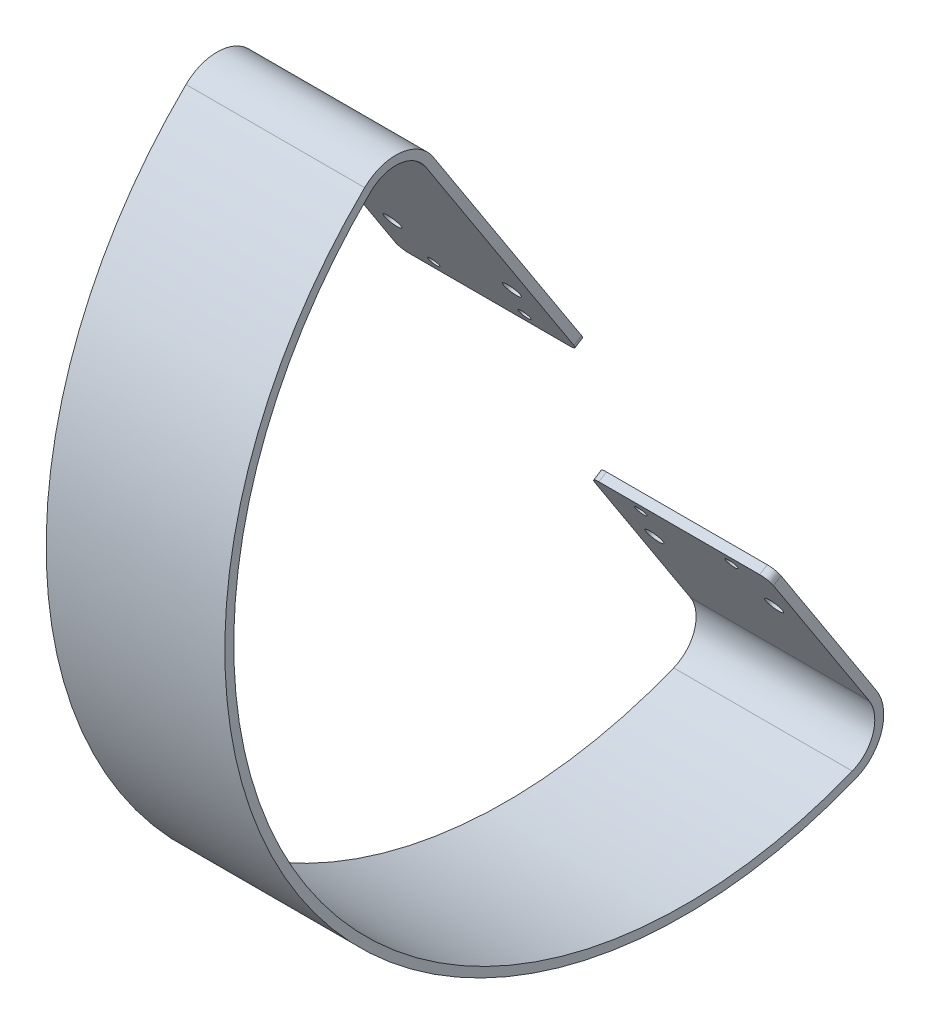
SolidWorks part; units mm, degrees
ref_plane "Front Plane" through (0, 0, 0) normal (0, 0, 1) x (1, 0, 0)
ref_plane "Top Plane" through (0, 0, 0) normal (0, 1, 0) x (1, 0, 0)
ref_plane "Right Plane" through (0, 0, 0) normal (1, 0, 0) x (0, 0, -1)
ref_plane "Plane1" through (1981.2, 0, 0) normal (1, 0, 0) x (0, 0, -1)
sketch "Sketch2" plane through (1981.2, 0, 0) normal (1, 0, 0) x (0, 0, -1)
  line L0 (221.3296, 149.9357) -> (209.5008, 142.2673) construction
  line L1 (221.3296, 149.9357) -> (209.184, 168.6708) construction
  line L2 (221.3296, 149.9357) -> (209.184, 168.6708) construction
  line L3 (273.5917, 69.3195) -> (285.7374, 50.5844) construction
  line L4 (273.5917, 69.3195) -> (285.7374, 50.5844) construction
  line L5 (220.4661, 151.2678) -> (176.9489, 218.3946)
  line L6 (274.4553, 67.9874) -> (303.0021, 23.953)
  line L7 (313.9939, 6.9977) -> (307.8258, 16.5121) construction
  line L8 (273.5917, 69.3195) -> (265.5737, 64.1215) construction
  line L9 (165.7975, 235.5961) -> (172.2848, 225.5893) construction
  line L10 (247.9458, 109.942) -> (151.6337, 47.5045) construction
  line L11 (151.6337, 47.5045) -> (142.0377, 41.2836) construction
  arc A0 (157.4526, 220.6047) -> (297.0616, 5.2526) centre (248.4911, 126.6943) ccw
  arc A1 (297.0616, 5.2526) -> (303.0021, 23.953) centre (292.3455, 17.0445) ccw
  arc A2 (176.9489, 218.3946) -> (157.4526, 220.6047) centre (166.2923, 211.4861) ccw
  spline S11 degree 3 poles (716.4378, 3936.626) (-41.01, 922.5586) (-45.8421, 102.7973) (199.57, -1.0271) (203.7349, -2.5525) (212.2057, -5.1923) (216.5116, -6.3067) (221.9842, -7.4366) (223.0832, -7.6494) (225.2905, -8.0483) (226.4002, -8.2347) (229.7298, -8.7513) (231.9491, -9.0392) (238.6058, -9.7364) (247.4783, -10.2233) (256.3445, -9.8408) (262.9919, -9.2245) (265.2072, -8.964) (268.5297, -8.4895) (269.6371, -8.3173) (271.8517, -7.9447) (272.9592, -7.7441) (278.4654, -6.6762) (282.7945, -5.61) (291.3052, -3.0674) (295.4869, -1.5909) (303.7034, 1.7715) (307.7383, 3.6574) (313.6773, 6.8016) (315.6425, 7.9051) (319.4945, 10.1955) (321.3853, 11.3842) (326.954, 15.0783) (334.1028, 20.3445) (340.7075, 26.2822) (345.4543, 30.9907) (347.0021, 32.6028) (349.271, 35.086) (350.0194, 35.9257) (351.4935, 37.6212) (352.2185, 38.4763) (355.7849, 42.7884) (358.4496, 46.3546) (363.4124, 53.7139) (365.7105, 57.5069) (369.9395, 65.3203) (371.8705, 69.3405) (374.0477, 74.5122) (374.4716, 75.5549) (375.2914, 77.6441) (375.6877, 78.6918) (376.8361, 81.8437) (377.548, 83.9569) (379.5247, 90.3317) (381.7375, 98.9252) (383.1139, 107.7043) (383.8268, 114.3594) (384.0111, 116.5896) (384.206, 119.9531) (384.2572, 121.077) (384.3321, 123.3185) (384.3557, 124.4376) (384.4056, 130.025) (384.2279, 134.4691) (383.4468, 143.3067) (382.8435, 147.7002) (381.2088, 156.4363) (380.1775, 160.7789) (378.6114, 166.1743) (378.2848, 167.25) (377.6073, 169.3868) (377.2561, 170.4491) (376.1655, 173.6179) (375.3891, 175.7062) (372.914, 181.8996) (371.0697, 185.9333) (366.9956, 193.8116) (364.7657, 197.6562) (361.1252, 203.278) (359.8623, 205.1277) (357.2357, 208.7777) (355.8817, 210.5644) (351.7057, 215.8037) (348.7675, 219.1395) (342.5889, 225.5033) (339.3485, 228.5312) (332.5628, 234.2766) (329.0156, 236.9953) (49.0165, 430.2441) (-881.9041, -433.1454) (-2551.1811, -2485.4465) knots -1.810739 -1.810739 -1.810739 -1.810739 0.03125 0.03125 0.0625 0.0625 0.09375 0.09375 0.101562 0.101562 0.109375 0.109375 0.125 0.125 0.15625 0.1875 0.1875 0.203125 0.203125 0.210937 0.210937 0.21875 0.21875 0.25 0.25 0.28125 0.28125 0.3125 0.3125 0.328125 0.328125 0.34375 0.34375 0.375 0.40625 0.40625 0.421875 0.421875 0.429687 0.429687 0.4375 0.4375 0.46875 0.46875 0.5 0.5 0.53125 0.53125 0.539063 0.539063 0.546875 0.546875 0.5625 0.5625 0.59375 0.625 0.625 0.640625 0.640625 0.648438 0.648438 0.65625 0.65625 0.6875 0.6875 0.71875 0.71875 0.75 0.75 0.757813 0.757813 0.765625 0.765625 0.78125 0.78125 0.8125 0.8125 0.84375 0.84375 0.859375 0.859375 0.875 0.875 0.90625 0.90625 0.9375 0.9375 0.96875 0.96875 3.30132 3.30132 3.30132 3.30132 only from (183.4088, 6.5279) to (313.8564, 246.6465)
  spline S12 degree 3 poles (183.4088, 6.5279) (187.3587, 4.3756) (191.3819, 2.437) (199.57, -1.0271) (203.7349, -2.5525) (212.2057, -5.1923) (216.5116, -6.3067) (221.9842, -7.4366) (223.0832, -7.6494) (225.2905, -8.0483) (226.4002, -8.2347) (229.7298, -8.7513) (231.9491, -9.0392) (238.6058, -9.7364) (247.4783, -10.2233) (256.3445, -9.8408) (262.9919, -9.2245) (265.2072, -8.964) (268.5297, -8.4895) (269.6371, -8.3173) (271.8517, -7.9447) (272.9592, -7.7441) (278.4654, -6.6762) (282.7945, -5.61) (291.3052, -3.0674) (295.4869, -1.5909) (303.7034, 1.7715) (307.7383, 3.6574) (313.6773, 6.8016) (315.6425, 7.9051) (319.4945, 10.1955) (321.3853, 11.3842) (326.954, 15.0783) (334.1028, 20.3445) (340.7075, 26.2822) (345.4543, 30.9907) (347.0021, 32.6028) (349.271, 35.086) (350.0194, 35.9257) (351.4935, 37.6212) (352.2185, 38.4763) (355.7849, 42.7884) (358.4496, 46.3546) (363.4124, 53.7139) (365.7105, 57.5069) (369.9395, 65.3203) (371.8705, 69.3405) (374.0477, 74.5122) (374.4716, 75.5549) (375.2914, 77.6441) (375.6877, 78.6918) (376.8361, 81.8437) (377.548, 83.9569) (379.5247, 90.3317) (381.7375, 98.9252) (383.1139, 107.7043) (383.8268, 114.3594) (384.0111, 116.5896) (384.206, 119.9531) (384.2572, 121.077) (384.3321, 123.3185) (384.3557, 124.4376) (384.4056, 130.025) (384.2279, 134.4691) (383.4468, 143.3067) (382.8435, 147.7002) (381.2088, 156.4363) (380.1775, 160.7789) (378.6114, 166.1743) (378.2848, 167.25) (377.6073, 169.3868) (377.2561, 170.4491) (376.1655, 173.6179) (375.3891, 175.7062) (372.914, 181.8996) (371.0697, 185.9333) (366.9956, 193.8116) (364.7657, 197.6562) (361.1252, 203.278) (359.8623, 205.1277) (357.2357, 208.7777) (355.8817, 210.5644) (351.7057, 215.8037) (348.7675, 219.1395) (342.5889, 225.5033) (339.3485, 228.5312) (332.5628, 234.2766) (329.0156, 236.9953) (321.6123, 242.1048) (317.7932, 244.4704) (313.8564, 246.6465) knots 0 0 0 0 0.03125 0.03125 0.0625 0.0625 0.09375 0.09375 0.101562 0.101562 0.109375 0.109375 0.125 0.125 0.15625 0.1875 0.1875 0.203125 0.203125 0.210937 0.210937 0.21875 0.21875 0.25 0.25 0.28125 0.28125 0.3125 0.3125 0.328125 0.328125 0.34375 0.34375 0.375 0.40625 0.40625 0.421875 0.421875 0.429687 0.429687 0.4375 0.4375 0.46875 0.46875 0.5 0.5 0.53125 0.53125 0.539063 0.539063 0.546875 0.546875 0.5625 0.5625 0.59375 0.625 0.625 0.640625 0.640625 0.648438 0.648438 0.65625 0.65625 0.6875 0.6875 0.71875 0.71875 0.75 0.75 0.757813 0.757813 0.765625 0.765625 0.78125 0.78125 0.8125 0.8125 0.84375 0.84375 0.859375 0.859375 0.875 0.875 0.90625 0.90625 0.9375 0.9375 0.96875 0.96875 1 1 1 1 construction
  spline S13 degree 3 poles (-242.5395, -3680.1608) (532.8048, -671.0788) (542.6093, 149.0677) (297.6784, 254.3238) (293.5061, 255.8778) (285.0171, 258.5726) (280.7003, 259.7133) (275.2117, 260.8746) (274.1094, 261.0936) (271.8953, 261.5048) (270.782, 261.6972) (267.443, 262.2314) (265.217, 262.5306) (258.5394, 263.2607) (249.6363, 263.7882) (240.7343, 263.4398) (234.0581, 262.8463) (231.8328, 262.593) (228.4949, 262.1285) (227.3823, 261.9595) (225.1571, 261.5931) (224.0452, 261.3957) (218.5166, 260.3429) (214.169, 259.2871) (205.6195, 256.7613) (201.4177, 255.2913) (193.1597, 251.9376) (189.1035, 250.054) (183.1315, 246.9097) (181.1566, 245.8063) (177.2874, 243.5165) (175.3879, 242.3277) (169.7931, 238.6317) (162.6093, 233.359) (155.9696, 227.4065) (151.1969, 222.6832) (149.6406, 221.0656) (147.359, 218.5732) (146.6064, 217.7303) (145.1266, 216.0311) (144.3986, 215.1739) (140.818, 210.8513) (138.1421, 207.2748) (133.1582, 199.8912) (130.8502, 196.0841) (126.6032, 188.2385) (124.6641, 184.2) (122.4784, 179.0026) (122.0536, 177.9566) (121.2326, 175.8611) (120.8357, 174.8103) (119.6855, 171.6484) (118.9728, 169.5282) (116.994, 163.1312) (115.8872, 158.8181) (114.0946, 150.0958) (113.4088, 145.6866) (112.7023, 138.9994) (112.5206, 136.758) (112.2671, 132.2503) (112.1964, 130.0028) (112.1486, 123.2788) (112.3356, 118.8209) (113.1385, 109.9533) (113.7544, 105.5437) (115.0024, 98.9659) (115.4726, 96.7794) (116.2603, 93.5089) (116.5366, 92.4203) (117.117, 90.2462) (117.4215, 89.1595) (119.0097, 83.7486) (120.4827, 79.5175) (123.8202, 71.2447) (125.6848, 67.2028) (129.8041, 59.3075) (132.0588, 55.454) (135.127, 50.7579) (135.7532, 49.8247) (137.0308, 47.9705) (137.6833, 47.0483) (139.6701, 44.3124) (141.0345, 42.5284) (145.2445, 37.2943) (151.1692, 30.6289) (157.7065, 24.5799) (162.8419, 20.2771) (164.5926, 18.8819) (167.2777, 16.8487) (168.1826, 16.1809) (170.0125, 14.8654) (170.9378, 14.2174) (443.8284, -171.8536) (1345.0037, 655.8308) (3034.7171, 2753.1631) knots -1.804531 -1.804531 -1.804531 -1.804531 0.03125 0.03125 0.0625 0.0625 0.09375 0.09375 0.101562 0.101562 0.109375 0.109375 0.125 0.125 0.15625 0.1875 0.1875 0.203125 0.203125 0.210937 0.210937 0.21875 0.21875 0.25 0.25 0.28125 0.28125 0.3125 0.3125 0.328125 0.328125 0.34375 0.34375 0.375 0.40625 0.40625 0.421875 0.421875 0.429687 0.429687 0.4375 0.4375 0.46875 0.46875 0.5 0.5 0.53125 0.53125 0.539062 0.539062 0.546875 0.546875 0.5625 0.5625 0.59375 0.59375 0.625 0.625 0.640625 0.640625 0.65625 0.65625 0.6875 0.6875 0.71875 0.71875 0.734375 0.734375 0.742187 0.742187 0.75 0.75 0.78125 0.78125 0.8125 0.8125 0.84375 0.84375 0.851562 0.851562 0.859375 0.859375 0.875 0.875 0.90625 0.9375 0.9375 0.953125 0.953125 0.960937 0.960937 0.96875 0.96875 3.24847 3.24847 3.24847 3.24847 only from (313.8564, 246.6465) to (183.4088, 6.5279)
  spline S14 degree 3 poles (313.8564, 246.6465) (309.9046, 248.8308) (305.8776, 250.8003) (297.6784, 254.3238) (293.5061, 255.8778) (285.0171, 258.5726) (280.7003, 259.7133) (275.2117, 260.8746) (274.1094, 261.0936) (271.8953, 261.5048) (270.782, 261.6972) (267.443, 262.2314) (265.217, 262.5306) (258.5394, 263.2607) (249.6363, 263.7882) (240.7343, 263.4398) (234.0581, 262.8463) (231.8328, 262.593) (228.4949, 262.1285) (227.3823, 261.9595) (225.1571, 261.5931) (224.0452, 261.3957) (218.5166, 260.3429) (214.169, 259.2871) (205.6195, 256.7613) (201.4177, 255.2913) (193.1597, 251.9376) (189.1035, 250.054) (183.1315, 246.9097) (181.1566, 245.8063) (177.2874, 243.5165) (175.3879, 242.3277) (169.7931, 238.6317) (162.6093, 233.359) (155.9696, 227.4065) (151.1969, 222.6832) (149.6406, 221.0656) (147.359, 218.5732) (146.6064, 217.7303) (145.1266, 216.0311) (144.3986, 215.1739) (140.818, 210.8513) (138.1421, 207.2748) (133.1582, 199.8912) (130.8502, 196.0841) (126.6032, 188.2385) (124.6641, 184.2) (122.4784, 179.0026) (122.0536, 177.9566) (121.2326, 175.8611) (120.8357, 174.8103) (119.6855, 171.6484) (118.9728, 169.5282) (116.994, 163.1312) (115.8872, 158.8181) (114.0946, 150.0958) (113.4088, 145.6866) (112.7023, 138.9994) (112.5206, 136.758) (112.2671, 132.2503) (112.1964, 130.0028) (112.1486, 123.2788) (112.3356, 118.8209) (113.1385, 109.9533) (113.7544, 105.5437) (115.0024, 98.9659) (115.4726, 96.7794) (116.2603, 93.5089) (116.5366, 92.4203) (117.117, 90.2462) (117.4215, 89.1595) (119.0097, 83.7486) (120.4827, 79.5175) (123.8202, 71.2447) (125.6848, 67.2028) (129.8041, 59.3075) (132.0588, 55.454) (135.127, 50.7579) (135.7532, 49.8247) (137.0308, 47.9705) (137.6833, 47.0483) (139.6701, 44.3124) (141.0345, 42.5284) (145.2445, 37.2943) (151.1692, 30.6289) (157.7065, 24.5799) (162.8419, 20.2771) (164.5926, 18.8819) (167.2777, 16.8487) (168.1826, 16.1809) (170.0125, 14.8654) (170.9378, 14.2174) (175.5978, 11.04) (179.444, 8.6885) (183.4088, 6.5279) knots 0 0 0 0 0.03125 0.03125 0.0625 0.0625 0.09375 0.09375 0.101562 0.101562 0.109375 0.109375 0.125 0.125 0.15625 0.1875 0.1875 0.203125 0.203125 0.210937 0.210937 0.21875 0.21875 0.25 0.25 0.28125 0.28125 0.3125 0.3125 0.328125 0.328125 0.34375 0.34375 0.375 0.40625 0.40625 0.421875 0.421875 0.429687 0.429687 0.4375 0.4375 0.46875 0.46875 0.5 0.5 0.53125 0.53125 0.539062 0.539062 0.546875 0.546875 0.5625 0.5625 0.59375 0.59375 0.625 0.625 0.640625 0.640625 0.65625 0.65625 0.6875 0.6875 0.71875 0.71875 0.734375 0.734375 0.742187 0.742187 0.75 0.75 0.78125 0.78125 0.8125 0.8125 0.84375 0.84375 0.851562 0.851562 0.859375 0.859375 0.875 0.875 0.90625 0.9375 0.9375 0.953125 0.953125 0.960937 0.960937 0.96875 0.96875 1 1 1 1 construction
  spline S15 degree 3 poles (-283.106, -3688.3408) (508.334, -662.837) (526.1426, 143.4053) (293.3653, 243.1749) (289.5491, 244.5923) (281.7849, 247.0493) (277.837, 248.0889) (272.8177, 249.1464) (271.8096, 249.3458) (269.7849, 249.7201) (268.7669, 249.8952) (265.7133, 250.3813) (263.6778, 250.6532) (257.5713, 251.316) (249.4303, 251.7922) (241.291, 251.468) (235.1872, 250.9213) (233.1527, 250.6884) (230.1011, 250.2617) (229.0839, 250.1066) (227.0497, 249.7703) (226.033, 249.5891) (220.9782, 248.6234) (217.0033, 247.6557) (209.1872, 245.3418) (205.3459, 243.9957) (197.7969, 240.9256) (194.0891, 239.2017) (188.6302, 236.3247) (186.8249, 235.315) (183.2875, 233.2197) (181.551, 232.132) (176.4364, 228.7505) (169.8693, 223.927) (163.7999, 218.4829) (159.4374, 214.1635) (158.0148, 212.6842) (155.9293, 210.4051) (155.2414, 209.6343) (153.8884, 208.0802) (153.2229, 207.2963) (149.9492, 203.3428) (147.5028, 200.0721) (142.9464, 193.3202) (140.8363, 189.8391) (136.9535, 182.6657) (135.1806, 178.9735) (133.1822, 174.2221) (132.7937, 173.2655) (132.0427, 171.3492) (131.6797, 170.3883) (130.6277, 167.4969) (129.9758, 165.5582) (128.1657, 159.7088) (127.1531, 155.7651) (125.5126, 147.7903) (124.8848, 143.7592) (124.2373, 137.6458) (124.0706, 135.5968) (123.8376, 131.4761) (123.7722, 129.4199) (123.7265, 123.2709) (123.896, 119.1943) (124.6269, 111.0857) (125.1883, 107.0537) (126.3265, 101.0393) (126.7553, 99.0401) (127.7134, 95.0532) (128.2432, 93.0636) (129.9829, 87.1241) (131.3277, 83.254) (134.375, 75.687) (136.0776, 71.9901) (139.8389, 64.7687) (141.8976, 61.2443) (144.6991, 56.9491) (145.2709, 56.0957) (146.4374, 54.3999) (147.0331, 53.5564) (148.8483, 51.0526) (150.0947, 49.42) (153.9409, 44.63) (159.3536, 38.5301) (165.3255, 32.9941) (170.0165, 29.0559) (171.6156, 27.7789) (174.0683, 25.9178) (174.8948, 25.3065) (176.5662, 24.1024) (177.4116, 23.509) (439.002, -155.2606) (1332.8814, 685.8356) (3014.0431, 2794.3665) knots -1.877287 -1.877287 -1.877287 -1.877287 0.03125 0.03125 0.0625 0.0625 0.09375 0.09375 0.101563 0.101563 0.109375 0.109375 0.125 0.125 0.15625 0.1875 0.1875 0.203125 0.203125 0.210938 0.210938 0.21875 0.21875 0.25 0.25 0.28125 0.28125 0.3125 0.3125 0.328125 0.328125 0.34375 0.34375 0.375 0.40625 0.40625 0.421875 0.421875 0.429688 0.429688 0.4375 0.4375 0.46875 0.46875 0.5 0.5 0.53125 0.53125 0.539063 0.539063 0.546875 0.546875 0.5625 0.5625 0.59375 0.59375 0.625 0.625 0.640625 0.640625 0.65625 0.65625 0.6875 0.6875 0.71875 0.71875 0.734375 0.734375 0.75 0.75 0.78125 0.78125 0.8125 0.8125 0.84375 0.84375 0.851563 0.851563 0.859375 0.859375 0.875 0.875 0.90625 0.9375 0.9375 0.953125 0.953125 0.960938 0.960938 0.96875 0.96875 3.360625 3.360625 3.360625 3.360625 only from (308.1647, 236.1696) to (188.8075, 16.4655)
  spline S16 degree 3 poles (308.1647, 236.1696) (304.5493, 238.1632) (300.8654, 239.9603) (293.3653, 243.1749) (289.5491, 244.5923) (281.7849, 247.0493) (277.837, 248.0889) (272.8177, 249.1464) (271.8096, 249.3458) (269.7849, 249.7201) (268.7669, 249.8952) (265.7133, 250.3813) (263.6778, 250.6532) (257.5713, 251.316) (249.4303, 251.7922) (241.291, 251.468) (235.1872, 250.9213) (233.1527, 250.6884) (230.1011, 250.2617) (229.0839, 250.1066) (227.0497, 249.7703) (226.033, 249.5891) (220.9782, 248.6234) (217.0033, 247.6557) (209.1872, 245.3418) (205.3459, 243.9957) (197.7969, 240.9256) (194.0891, 239.2017) (188.6302, 236.3247) (186.8249, 235.315) (183.2875, 233.2197) (181.551, 232.132) (176.4364, 228.7505) (169.8693, 223.927) (163.7999, 218.4829) (159.4374, 214.1635) (158.0148, 212.6842) (155.9293, 210.4051) (155.2414, 209.6343) (153.8884, 208.0802) (153.2229, 207.2963) (149.9492, 203.3428) (147.5028, 200.0721) (142.9464, 193.3202) (140.8363, 189.8391) (136.9535, 182.6657) (135.1806, 178.9735) (133.1822, 174.2221) (132.7937, 173.2655) (132.0427, 171.3492) (131.6797, 170.3883) (130.6277, 167.4969) (129.9758, 165.5582) (128.1657, 159.7088) (127.1531, 155.7651) (125.5126, 147.7903) (124.8848, 143.7592) (124.2373, 137.6458) (124.0706, 135.5968) (123.8376, 131.4761) (123.7722, 129.4199) (123.7265, 123.2709) (123.896, 119.1943) (124.6269, 111.0857) (125.1883, 107.0537) (126.3265, 101.0393) (126.7553, 99.0401) (127.7134, 95.0532) (128.2432, 93.0636) (129.9829, 87.1241) (131.3277, 83.254) (134.375, 75.687) (136.0776, 71.9901) (139.8389, 64.7687) (141.8976, 61.2443) (144.6991, 56.9491) (145.2709, 56.0957) (146.4374, 54.3999) (147.0331, 53.5564) (148.8483, 51.0526) (150.0947, 49.42) (153.9409, 44.63) (159.3536, 38.5301) (165.3255, 32.9941) (170.0165, 29.0559) (171.6156, 27.7789) (174.0683, 25.9178) (174.8948, 25.3065) (176.5662, 24.1024) (177.4116, 23.509) (181.6698, 20.599) (185.1844, 18.445) (188.8075, 16.4655) knots 0 0 0 0 0.03125 0.03125 0.0625 0.0625 0.09375 0.09375 0.101563 0.101563 0.109375 0.109375 0.125 0.125 0.15625 0.1875 0.1875 0.203125 0.203125 0.210938 0.210938 0.21875 0.21875 0.25 0.25 0.28125 0.28125 0.3125 0.3125 0.328125 0.328125 0.34375 0.34375 0.375 0.40625 0.40625 0.421875 0.421875 0.429688 0.429688 0.4375 0.4375 0.46875 0.46875 0.5 0.5 0.53125 0.53125 0.539063 0.539063 0.546875 0.546875 0.5625 0.5625 0.59375 0.59375 0.625 0.625 0.640625 0.640625 0.65625 0.65625 0.6875 0.6875 0.71875 0.71875 0.734375 0.734375 0.75 0.75 0.78125 0.78125 0.8125 0.8125 0.84375 0.84375 0.851563 0.851563 0.859375 0.859375 0.875 0.875 0.90625 0.9375 0.9375 0.953125 0.953125 0.960938 0.960938 0.96875 0.96875 1 1 1 1 construction
  spline S17 degree 3 poles (-2751.1525, 2792.7474) (1122.9295, -127.9602) (498.065, 247.5508) (102.2279, 91.7606) (97.9404, 89.9983) (91.5629, 87.2263) (89.446, 86.281) (86.29, 84.8167) (85.2412, 84.3208) (13.5509, 49.5235) (-37.8649, -30.7706) (1405.2472, -3686.3529) knots -22.187167 -22.187167 -22.187167 -22.187167 0.5 0.5 0.75 0.75 0.875 0.875 0.9375 0.9375 5.166072 5.166072 5.166072 5.166072 only from (132.7178, 102.9159) to (81.0819, 82.252)
  spline S18 degree 3 poles (132.7178, 102.9159) (123.9131, 99.9934) (115.171, 96.8546) (102.2279, 91.7606) (97.9404, 89.9983) (91.5629, 87.2263) (89.446, 86.281) (86.29, 84.8167) (85.2412, 84.3208) (83.1528, 83.3072) (82.1129, 82.7903) (81.0819, 82.252) knots 0 0 0 0 0.5 0.5 0.75 0.75 0.875 0.875 0.9375 0.9375 1 1 1 1 construction
  spline S19 degree 3 poles (764.9531, 3943.1565) (-14.832, 914.4258) (-29.4722, 108.4213) (203.5969, 9.5325) (207.4088, 8.132) (215.1622, 5.7075) (219.1037, 4.6835) (224.1135, 3.6445) (225.1196, 3.4487) (227.1403, 3.0817) (228.1562, 2.9102) (231.2042, 2.4345) (233.2358, 2.1693) (239.3299, 1.5259) (247.4528, 1.0737) (255.571, 1.4181) (261.6577, 1.9783) (263.6863, 2.2155) (266.7288, 2.6481) (267.7429, 2.8051) (269.7709, 3.1451) (270.785, 3.3281) (275.8265, 4.3028) (279.7904, 5.2766) (287.5837, 7.6004) (291.413, 8.9503) (298.9375, 12.0256) (302.6327, 13.7509) (308.0721, 16.6279) (309.8717, 17.6376) (313.3989, 19.7332) (315.1302, 20.8209) (320.2294, 24.2012) (326.7758, 29.0209) (332.8245, 34.4563) (337.1717, 38.7669) (338.5892, 40.2429) (340.6672, 42.5166) (341.3527, 43.2855) (342.7023, 44.8374) (343.3661, 45.6202) (346.6313, 49.5673) (349.0711, 52.832) (353.6151, 59.5695) (355.7193, 63.0423) (359.5915, 70.1966) (361.3595, 73.878) (363.3529, 78.6142) (363.7409, 79.5689) (364.4911, 81.4814) (364.8538, 82.4405) (365.9048, 85.326) (366.5562, 87.2606) (368.3651, 93.0968) (370.3898, 100.9649) (371.6483, 109.0038) (372.2996, 115.0983) (372.4678, 117.1407) (372.6454, 120.2209) (372.692, 121.2497) (372.7599, 123.3015) (372.7812, 124.3259) (372.8253, 129.4407) (372.6612, 133.5091) (371.9432, 141.5999) (371.3893, 145.6224) (369.8891, 153.6213) (368.9428, 157.5976) (367.2188, 163.5263) (366.5969, 165.4835) (365.2638, 169.3503) (364.552, 171.2616) (362.2831, 176.9303) (360.5926, 180.6223) (356.858, 187.8336) (354.8139, 191.3527) (351.4766, 196.4989) (350.3187, 198.1924) (347.911, 201.5331) (346.671, 203.1668) (342.8449, 207.9599) (337.4608, 214.0634) (331.5223, 219.6036) (326.8586, 223.5454) (325.269, 224.8237) (322.0186, 227.3081) (320.3563, 228.5151) (55.1067, 411.2126) (-858.655, -454.0579) (-2525.9478, -2532.4739) knots -1.881423 -1.881423 -1.881423 -1.881423 0.03125 0.03125 0.0625 0.0625 0.09375 0.09375 0.101562 0.101562 0.109375 0.109375 0.125 0.125 0.15625 0.1875 0.1875 0.203125 0.203125 0.210938 0.210938 0.21875 0.21875 0.25 0.25 0.28125 0.28125 0.3125 0.3125 0.328125 0.328125 0.34375 0.34375 0.375 0.40625 0.40625 0.421875 0.421875 0.429687 0.429687 0.4375 0.4375 0.46875 0.46875 0.5 0.5 0.53125 0.53125 0.539062 0.539062 0.546875 0.546875 0.5625 0.5625 0.59375 0.625 0.625 0.640625 0.640625 0.648437 0.648437 0.65625 0.65625 0.6875 0.6875 0.71875 0.71875 0.75 0.75 0.765625 0.765625 0.78125 0.78125 0.8125 0.8125 0.84375 0.84375 0.859375 0.859375 0.875 0.875 0.90625 0.9375 0.9375 0.953125 0.953125 0.96875 0.96875 3.397555 3.397555 3.397555 3.397555 only from (188.8075, 16.4655) to (308.1647, 236.1696)
  spline S20 degree 3 poles (188.8075, 16.4655) (192.4217, 14.4908) (196.1034, 12.7119) (203.5969, 9.5325) (207.4088, 8.132) (215.1622, 5.7075) (219.1037, 4.6835) (224.1135, 3.6445) (225.1196, 3.4487) (227.1403, 3.0817) (228.1562, 2.9102) (231.2042, 2.4345) (233.2358, 2.1693) (239.3299, 1.5259) (247.4528, 1.0737) (255.571, 1.4181) (261.6577, 1.9783) (263.6863, 2.2155) (266.7288, 2.6481) (267.7429, 2.8051) (269.7709, 3.1451) (270.785, 3.3281) (275.8265, 4.3028) (279.7904, 5.2766) (287.5837, 7.6004) (291.413, 8.9503) (298.9375, 12.0256) (302.6327, 13.7509) (308.0721, 16.6279) (309.8717, 17.6376) (313.3989, 19.7332) (315.1302, 20.8209) (320.2294, 24.2012) (326.7758, 29.0209) (332.8245, 34.4563) (337.1717, 38.7669) (338.5892, 40.2429) (340.6672, 42.5166) (341.3527, 43.2855) (342.7023, 44.8374) (343.3661, 45.6202) (346.6313, 49.5673) (349.0711, 52.832) (353.6151, 59.5695) (355.7193, 63.0423) (359.5915, 70.1966) (361.3595, 73.878) (363.3529, 78.6142) (363.7409, 79.5689) (364.4911, 81.4814) (364.8538, 82.4405) (365.9048, 85.326) (366.5562, 87.2606) (368.3651, 93.0968) (370.3898, 100.9649) (371.6483, 109.0038) (372.2996, 115.0983) (372.4678, 117.1407) (372.6454, 120.2209) (372.692, 121.2497) (372.7599, 123.3015) (372.7812, 124.3259) (372.8253, 129.4407) (372.6612, 133.5091) (371.9432, 141.5999) (371.3893, 145.6224) (369.8891, 153.6213) (368.9428, 157.5976) (367.2188, 163.5263) (366.5969, 165.4835) (365.2638, 169.3503) (364.552, 171.2616) (362.2831, 176.9303) (360.5926, 180.6223) (356.858, 187.8336) (354.8139, 191.3527) (351.4766, 196.4989) (350.3187, 198.1924) (347.911, 201.5331) (346.671, 203.1668) (342.8449, 207.9599) (337.4608, 214.0634) (331.5223, 219.6036) (326.8586, 223.5454) (325.269, 224.8237) (322.0186, 227.3081) (320.3563, 228.5151) (315.2698, 232.0185) (311.7712, 234.1809) (308.1647, 236.1696) knots 0 0 0 0 0.03125 0.03125 0.0625 0.0625 0.09375 0.09375 0.101562 0.101562 0.109375 0.109375 0.125 0.125 0.15625 0.1875 0.1875 0.203125 0.203125 0.210938 0.210938 0.21875 0.21875 0.25 0.25 0.28125 0.28125 0.3125 0.3125 0.328125 0.328125 0.34375 0.34375 0.375 0.40625 0.40625 0.421875 0.421875 0.429687 0.429687 0.4375 0.4375 0.46875 0.46875 0.5 0.5 0.53125 0.53125 0.539062 0.539062 0.546875 0.546875 0.5625 0.5625 0.59375 0.625 0.625 0.640625 0.640625 0.648437 0.648437 0.65625 0.65625 0.6875 0.6875 0.71875 0.71875 0.75 0.75 0.765625 0.765625 0.78125 0.78125 0.8125 0.8125 0.84375 0.84375 0.859375 0.859375 0.875 0.875 0.90625 0.9375 0.9375 0.953125 0.953125 0.96875 0.96875 1 1 1 1 construction
  spline S21 degree 3 poles (2769.9179, -2964.6264) (54.3339, -168.8273) (38.2566, -57.489) (83.8558, -5.9808) (84.5785, -5.1969) (86.7794, -2.8779) (88.2901, -1.3751) (91.3667, 1.5757) (92.9329, 3.0232) (96.1079, 5.8762) (97.7165, 7.2812) (102.5853, 11.4344) (105.8915, 14.125) (112.6011, 19.3806) (116.0049, 21.9449) (122.8996, 26.9607) (126.3922, 29.4128) (133.4527, 34.2065) (137.0182, 36.5462) (646.9668, 360.422) (1813.8639, -388.0279) (148.3469, 3451.8328) knots -1.951853 -1.951853 -1.951853 -1.951853 0.03125 0.03125 0.0625 0.0625 0.125 0.125 0.1875 0.1875 0.25 0.25 0.375 0.375 0.5 0.5 0.625 0.625 0.75 0.75 18.337148 18.337148 18.337148 18.337148 only from (81.0819, -9.2325) to (162.6006, 51.9137)
  spline S22 degree 3 poles (81.0819, -9.2325) (81.7487, -8.3931) (82.4409, -7.5789) (83.8558, -5.9808) (84.5785, -5.1969) (86.7794, -2.8779) (88.2901, -1.3751) (91.3667, 1.5757) (92.9329, 3.0232) (96.1079, 5.8762) (97.7165, 7.2812) (102.5853, 11.4344) (105.8915, 14.125) (112.6011, 19.3806) (116.0049, 21.9449) (122.8996, 26.9607) (126.3922, 29.4128) (133.4527, 34.2065) (137.0182, 36.5462) (147.8148, 43.4033) (155.1459, 47.7585) (162.6006, 51.9137) knots 0 0 0 0 0.03125 0.03125 0.0625 0.0625 0.125 0.125 0.1875 0.1875 0.25 0.25 0.375 0.375 0.5 0.5 0.625 0.625 0.75 0.75 1 1 1 1 construction
  spline S23 degree 3 poles (207.2453, 83.5564) (260.0163, 2.1551) (341.4175, 54.9261) (288.6465, 136.3274) (235.8755, 217.7287) (154.4742, 164.9577) (207.2453, 83.5564) (260.0163, 2.1551) (341.4175, 54.9261) knots -0.5 0 0 0 0.5 0.5 0.5 1 1 1 1.5 1.5 1.5 weights 1 0.333333 0.333333 1 0.333333 0.333333 1 0.333333 0.333333 only from (207.2453, 83.5564) to (207.2453, 83.5564) construction
  spline S24 degree 3 poles (207.2453, 83.5564) (260.0163, 2.1551) (341.4175, 54.9261) (288.6465, 136.3274) (235.8755, 217.7287) (154.4742, 164.9577) (207.2453, 83.5564) (260.0163, 2.1551) (341.4175, 54.9261) knots -0.5 0 0 0 0.5 0.5 0.5 1 1 1 1.5 1.5 1.5 weights 1 0.333333 0.333333 1 0.333333 0.333333 1 0.333333 0.333333 only from (207.2453, 83.5564) to (207.2453, 83.5564) construction
  point P19 (169.0411, 230.5927)
  point P22 (310.9099, 11.7549)
  point P29 (146.8357, 44.394)
  point P33 (310.9099, 11.7549)
  point P36 (169.0411, 230.5927)
  dimension "D4" = 12.7
  dimension "D1" = 0
  dimension "D2" = 1.5875
  dimension "D3" = 1.5875
extrude "Extrude-Thin1" add sketch "Sketch2" along normal mid plane 50.8 thin contours L5 A2 A0 A1 L6
sketch "Sketch5" plane through (0, 145.3932, -224.2745) normal (0, 0.544, -0.8391) x (-1, 0, 0)
  ellipse E0 centre (-1997.9063, -111.0782) end of major axis (-2000.2876, -111.0782) minor radius 2.3812 construction
  ellipse E1 centre (-1963.9063, -111.0783) end of major axis (-1966.2876, -111.0783) minor radius 2.3812 construction
  ellipse E2 centre (-1967.8405, -96.6615) end of major axis (-1966.2898, -96.6615) minor radius 1.5506 construction
  ellipse E3 centre (-1993.6563, -96.6614) end of major axis (-1992.0101, -96.6614) minor radius 1.6462 construction
  ellipse E4 centre (-1967.8401, 11.5049) end of major axis (-1969.3908, 11.5049) minor radius 1.5506 construction
  ellipse E5 centre (-1993.6559, 11.505) end of major axis (-1995.3021, 11.505) minor radius 1.6462 construction
  ellipse E6 centre (-1963.9059, 25.9217) end of major axis (-1966.2871, 25.9217) minor radius 2.3812 construction
  ellipse E7 centre (-1997.9059, 25.9218) end of major axis (-2000.2871, 25.9218) minor radius 2.3812 construction
  ellipse E8 centre (-1997.9063, -111.0782) end of major axis (-2000.2876, -111.0782) minor radius 2.3812
  ellipse E9 centre (-1963.9063, -111.0783) end of major axis (-1966.2876, -111.0783) minor radius 2.3812
  ellipse E10 centre (-1967.8405, -96.6615) end of major axis (-1966.2898, -96.6615) minor radius 1.5506
  ellipse E11 centre (-1993.6563, -96.6614) end of major axis (-1992.0101, -96.6614) minor radius 1.6462
  ellipse E12 centre (-1967.8401, 11.5049) end of major axis (-1969.3908, 11.5049) minor radius 1.5506
  ellipse E13 centre (-1993.6559, 11.505) end of major axis (-1995.3021, 11.505) minor radius 1.6462
  ellipse E14 centre (-1963.9059, 25.9217) end of major axis (-1966.2871, 25.9217) minor radius 2.3812
  ellipse E15 centre (-1997.9059, 25.9218) end of major axis (-2000.2871, 25.9218) minor radius 2.3812
extrude "Cut-Extrude1" cut sketch "Sketch5" against normal up to surface (88.289 mm away)
fillet "Fillet1" radius 2.54 4 edges at (2006.6, 67.2965, -273.3896) (1955.8, 67.2965, -273.3896) (2006.6, 150.577, -219.4004) (1955.8, 150.577, -219.4004)
equation "\"D3@Sketch2\"=\"D2@Sketch2\""
